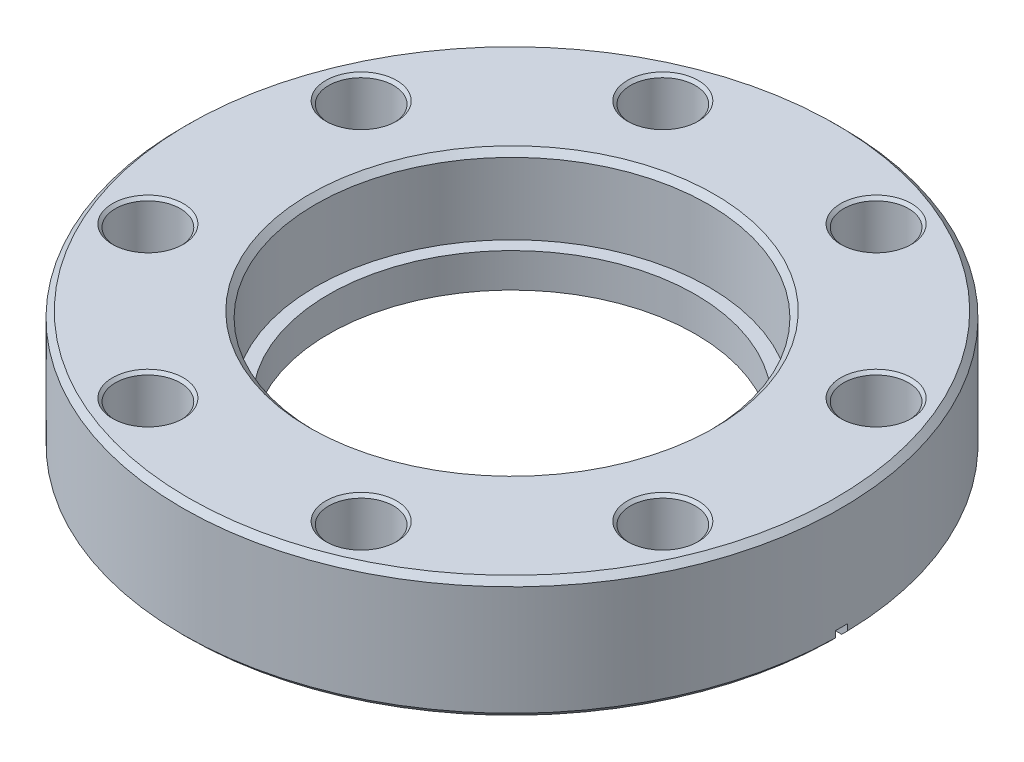
SolidWorks part; units mm, degrees
ref_plane "Front Plane" through (0, 0, 0) normal (0, 0, 1) x (1, 0, 0)
ref_plane "Top Plane" through (0, 0, 0) normal (0, 1, 0) x (1, 0, 0)
ref_plane "Right Plane" through (0, 0, 0) normal (1, 0, 0) x (0, 0, -1)
sketch "Sketch1" plane through (0, 0, 0) normal (0, 1, 0) x (1, 0, 0)
  circle A0 centre (0, 0) radius 42.799
  circle A1 centre (0, 0) radius 23.8125
  dimension "D1" = 85.598
  dimension "D2" = 47.625
extrude "Boss-Extrude1" add sketch "Sketch1" along normal blind 15.748
sketch "Sketch2" plane through (0, 15.748, 0) normal (0, 1, 0) x (-1, 0, 0)
  circle A0 centre (0, 0) radius 25.527
  dimension "D1" = 51.054
extrude "Cut-Extrude1" cut sketch "Sketch2" against normal blind 10.033
chamfer "Chamfer1" distance 0.762 angle 45 3 edges at (0, 0, 42.799) (0, 15.748, 25.527) (0, 15.748, 42.799)
sketch "Sketch5" plane through (0, 0, 0) normal (0, 0, -1) x (1, 0, 0)
  line L5 (0, 0) -> (-30.9499, 0)
  line L6 (42.037, 0) -> (-42.037, 0) construction
  line L7 (0, -1.27) -> (0, 0)
  line L8 (-27.94, -1.27) -> (0, -1.27)
  line L9 (-27.94, -0.6604) -> (-27.94, -1.27)
  line L10 (-30.9499, -1.7551) -> (-27.94, -0.6604)
  line L11 (-30.9499, 0) -> (-30.9499, -1.7551)
  dimension "D2" = 27.94
  dimension "D3" = 30.9499
  dimension "D4" = 1.7551
  dimension "D5" = 0.6096
  dimension "D6" = 1.27
revolve "Cut-Revolve1" cut sketch "Sketch5" angle 360 about axis through (0, 15.748, 0) along (0, -1, 0)
sketch "Sketch3" plane through (0, 0, 0) normal (0, -1, 0) x (1, 0, 0)
  line L0 (0, 0) -> (-13.8512, 33.4398) construction
  line L1 (0, 0) -> (0, 42.037) construction
  circle A0 centre (-13.8512, 33.4398) radius 4.2164
  circle A1 centre (0, 0) radius 42.037 construction
  dimension "D1" = 8.4328
  dimension "D2" = 36.195
  dimension "D3" = 22.5
extrude "Cut-Extrude2" cut sketch "Sketch3" against normal through all
chamfer "Chamfer2" distance 0.381 angle 45 2 edges at (-13.8512, 15.748, 29.2234) (-13.8512, 0, 29.2234)
pattern_circular "CirPattern1" count 8 every 45 about axis through (0, 0, 0) along (0, 1, 0) of "Cut-Extrude2", "Chamfer2"
sketch "Sketch6" plane through (0, 0, 0) normal (0, 0, 1) x (1, 0, 0)
  line L0 (0, 0) -> (0, -0.6556) construction
  line L1 (0, -0.6556) -> (-42.799, -0.6556) construction
  line L2 (-42.799, 1.5874) -> (-42.799, -0.6556)
  line L3 (-42.799, 1.5874) -> (0, -0.6556) construction
  line L4 (30.1275, 0.9233) -> (42.799, 1.5874)
  line L5 (-42.799, -0.6556) -> (-30.1275, -0.6556)
  line L6 (-30.1275, -0.6556) -> (-30.1275, 0.9233)
  line L7 (-30.1275, 0.9233) -> (-42.799, 1.5874)
  line L8 (30.1275, -0.6556) -> (30.1275, 0.9233)
  line L9 (42.799, -0.6556) -> (30.1275, -0.6556)
  line L10 (42.799, 1.5874) -> (42.799, -0.6556)
  dimension "D1" = 0.6556
  dimension "D2" = 3
extrude "Cut-Extrude3" cut sketch "Sketch6" against normal mid plane 1.5875
